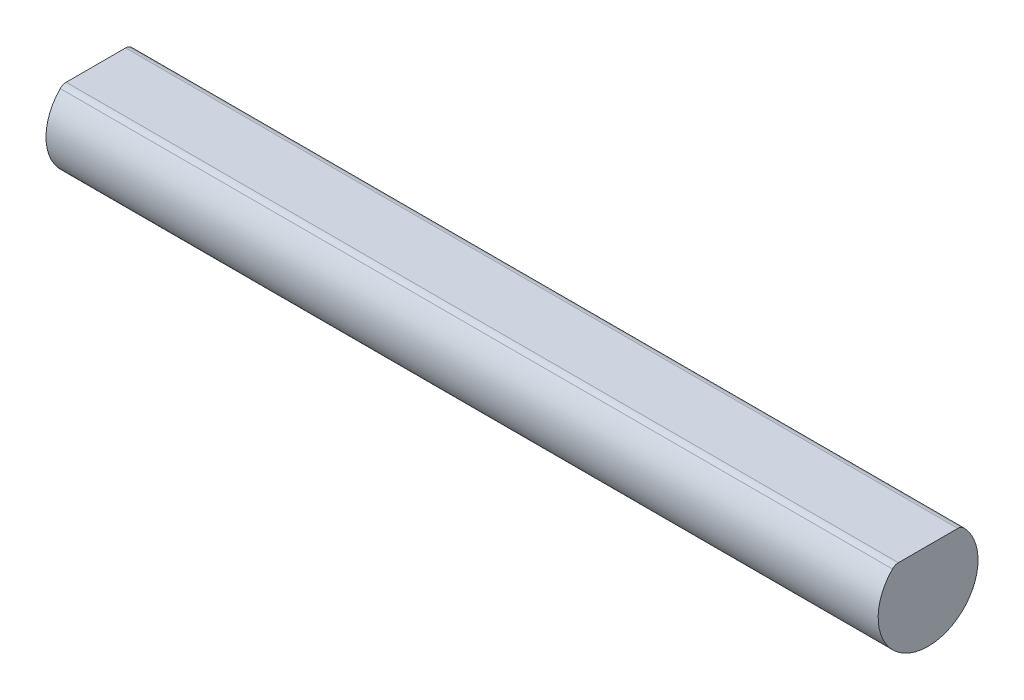
SolidWorks part; units mm, degrees
ref_plane "Front Plane" through (0, 0, 0) normal (0, 0, 1) x (1, 0, 0)
ref_plane "Top Plane" through (0, 0, 0) normal (0, 1, 0) x (1, 0, 0)
ref_plane "Right Plane" through (0, 0, 0) normal (1, 0, 0) x (0, 0, -1)
sketch "Sketch1" plane through (0, 0, 0) normal (1, 0, 0) x (0, 0, -1)
  circle A0 centre (0, 0) radius 6
  dimension "D1" = 12
extrude "Boss-Extrude1" add sketch "Sketch1" along normal blind 100
sketch "Sketch2" plane through (100, 0, 0) normal (1, 0, 0) x (0, 0, -1)
  line L0 (0, 6) -> (0, -6) construction
  line L1 (0, 6.6) -> (0, -6.6) construction
  line L2 (-3.9686, 4.5) -> (3.9686, 4.5)
  line L3 (-3.9686, 4.5) -> (-3.9686, 6.0994)
  line L4 (-3.9686, 6.0994) -> (3.9686, 6.0994)
  line L5 (3.9686, 6.1902) -> (3.9686, 4.5)
  circle A0 centre (0, 0) radius 6 construction
  point P6 (0, 4.5)
  circle M2 centre (0, 0) radius 6
  dimension "D1" = 1.5
extrude "Cut-Extrude1" cut sketch "Sketch2" against normal through all contours L5 L4 L3 M2 | L0 L2 M2 | L0 L2 M2
fillet "Fillet1" radius 1 2 edges at (50, 4.5, 3.9686) (50, 4.5, -3.9686)
